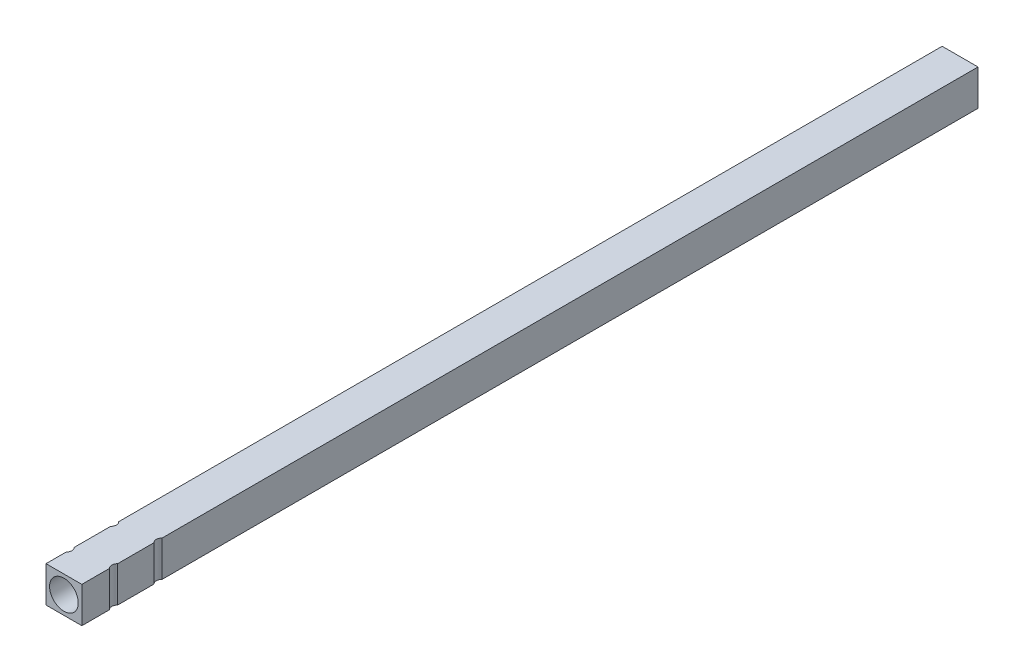
SolidWorks part; units mm, degrees
ref_plane "Front" through (0, 0, 0) normal (0, 0, 1) x (1, 0, 0)
ref_plane "Top" through (0, 0, 0) normal (0, 1, 0) x (1, 0, 0)
ref_plane "Right" through (0, 0, 0) normal (1, 0, 0) x (0, 0, -1)
sketch "Sketch1" plane through (0, 0, 0) normal (0, 0, 1) x (1, 0, 0)
  line B0 (-5, 5) -> (-5, -5)
  line B1 (-5, 5) -> (5, 5)
  line B2 (5, 5) -> (5, -5)
  line B3 (-5, -5) -> (5, -5)
  line B4 (-5, 5) -> (5, -5) construction
  line B5 (5, 5) -> (-5, -5) construction
  circle B6 centre (0, 0) radius 4
sketch_block_instance "Block-10mm Carbon-1"
sketch_block "Block-10mm Carbon" parameters "D2"=8, "D1"=10
extrude "Boss-Extrude1" add sketch "Sketch1" along normal blind 250 contours B1
sketch "Sketch2" plane through (0, -5, 0) normal (0, -1, 0) x (1, 0, 0)
  line L0 (-5, 250) -> (5, 250) construction
  line L1 (0, 236) -> (0, 250) construction
  line L2 (-6.1193, 230.8469) -> (-6.1193, 228.7333) construction
  line L3 (-6.1193, 243.2667) -> (6.1193, 228.7333) construction
  line L4 (-6.1193, 230.8469) -> (6.1193, 241.1531) construction
  line L5 (-6.1193, 228.7333) -> (6.1193, 228.7333) construction
  line L6 (-5, 250) -> (-5, 0) construction
  circle A0 centre (0, 236) radius 14 construction
  circle A1 centre (-6.1193, 243.2667) radius 1.6
  circle A2 centre (6.1193, 228.7333) radius 1.6
  circle A3 centre (-6.1193, 230.8469) radius 1.6
  circle A4 centre (6.1193, 241.1531) radius 1.6
  point P16 (0, 228.7333)
  dimension "D1" = 28
  dimension "D5" = 3.2
  dimension "D2" = 19
  dimension "D3" = 16
extrude "Cut-Extrude1" cut sketch "Sketch2" against normal through all
